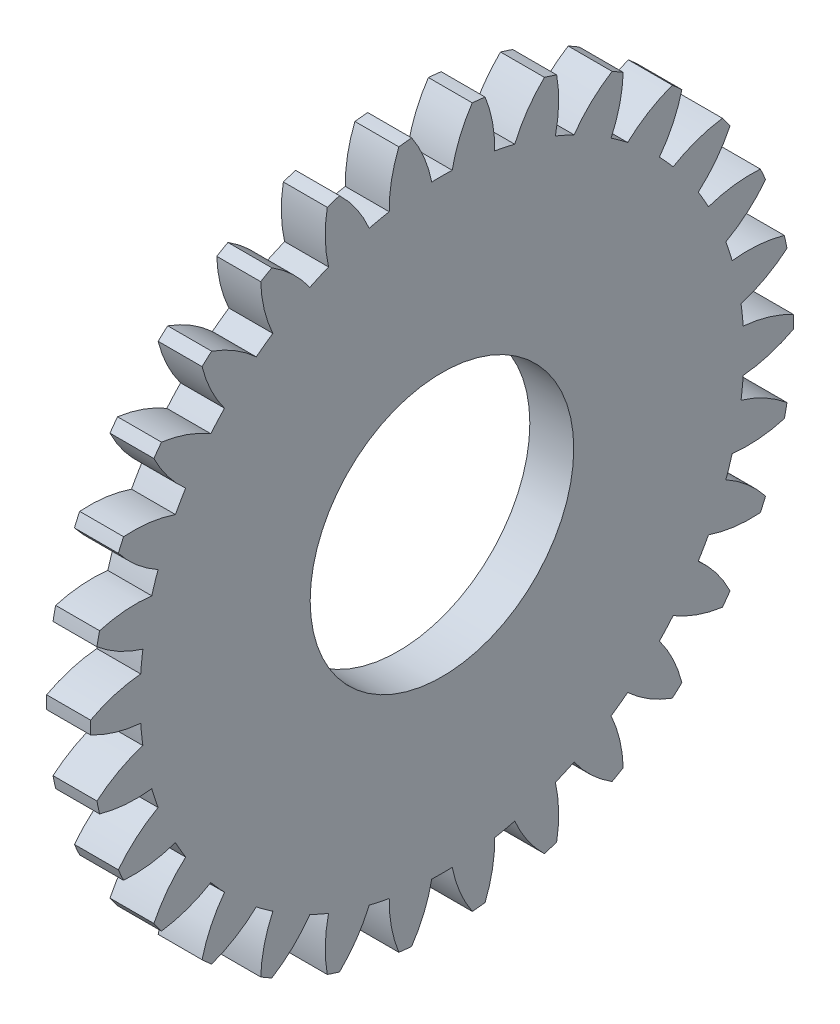
SolidWorks part; units mm, degrees
ref_plane "Plane1" through (0, 0, 0) normal (0, 0, 1) x (1, 0, 0)
ref_plane "Plane2" through (0, 0, 0) normal (0, 1, 0) x (1, 0, 0)
ref_plane "Plane3" through (0, 0, 0) normal (1, 0, 0) x (0, 0, -1)
other "Configuration Table"
sketch "HoldingSke" plane through (0, 0, 0) normal (0, 1, 0) x (1, 0, 0)
  line L0 (0, 0) -> (0.866, -0.5)
  line L1 (-15, 0) -> (100, 0) construction
  line L2 (0, 0) -> (-2.1039, 2.3779)
  line L3 (0, 0) -> (-11.863, 4.5341)
  line L4 (0, 0) -> (7.479, 4.318)
  line L5 (0, 0) -> (-46.8476, -17.4728)
  line L6 (0, 0) -> (-1.6579, -1.1186)
  line L7 (-2.1039, 2.3779) -> (8.6586, 51.2059)
  line L8 (-76.2, 54.61) -> (-73.9, 54.61)
  line L9 (-71.009, 38.7566) -> (-53.1078, 45.2721)
  line L10 (-76.2, 71.12) -> (104.1128, 71.12)
  line L11 (0, 0) -> (-2, 0)
  line L12 (-76.2, 101.6) -> (-76.162, 101.6)
  line L13 (24.9733, 27.94) -> (52.9518, 28.4284)
  line L14 (24.9733, 27.94) -> (24.9743, 27.94)
  line L15 (24.9733, 27.94) -> (100.4006, 29.5858)
  line L16 (-63.627, -1) -> (-12.827, -1)
  circle A0 centre (0, 0) radius 6
  circle A1 centre (0, 0) radius 13.749
  circle A2 centre (0, 0) radius 37.5
  circle A3 centre (0, 0) radius 6
  dimension "MHD" = 27.498
  dimension "Hub_dia" = 75
  dimension "Bore" = 12
  dimension "MBD" = 12
  dimension "Num_teeth" = 30
  dimension "Pitch" = 1
  dimension "Overall_len" = 50
  dimension "Show_teeth" = 30
  dimension "Thickness" = 2
  dimension "OAL" = 50.0001
  dimension "T_dim" = 2.3
  dimension "Ap" = 20
  dimension "H" = 19.05
  dimension "Pitch_radius" = 180.3128
  dimension "Width" = 2
  dimension "Backlash" = 0.038
  dimension "Addendum_fac" = 1
  dimension "Dedendum_fac" = 1.25
  dimension "Clearance_fac" = 0.25
  dimension "Dedendum_add" = 0.001
  dimension "Module" = 1
sketch "BasProSke" plane through (0, 0, 0) normal (0, 1, 0) x (1, 0, 0)
  line L0 (-10, 0) -> (60, 0) construction
  line L1 (0, 0) -> (0, 16)
  line L2 (0, 0) -> (2, 0)
  line L3 (2, 0) -> (2, 16)
  line L4 (2, 16) -> (0, 16)
  dimension "Thickness" = 2
  dimension "Diameter" = 32
revolve "Base-Revolve" add sketch "BasProSke" angle 360 about L0
sketch "TooCutSke" plane through (0, 0, 0) normal (1, 0, 0) x (0, 0, -1)
  line L1 (0, 0) -> (0, 107) construction
  line L2 (0, 0) -> (-0.8515, 14.9758) construction
  line L3 (0, 0) -> (-3.1323, 29.8014) construction
  line L4 (-0.8515, 14.9758) -> (-1.5661, 14.9007) construction
  arc A0 (0.4664, 13.7411) -> (-0.4664, 13.7411) centre (0, 0) ccw
  arc A1 (1.3975, 15.9644) -> (-1.3975, 15.9644) centre (0, 0) ccw
  circle A2 centre (0, 0) radius 15 construction
  circle A3 centre (0, 0) radius 14.0954 construction
  arc A4 (-0.4664, 13.7411) -> (-1.3975, 15.9644) centre (-6.3534, 12.5823) ccw
  arc A5 (1.3975, 15.9644) -> (0.4664, 13.7411) centre (6.3534, 12.5823) ccw
  dimension "Root_dia" = 27.498
  dimension "Overcut_dia" = 32.0508
  dimension "Pitch_dia" = 30
  dimension "Base_dia" = 28.1908
  dimension "Flank_rad" = 6
  dimension "Half_ang" = 6
  dimension "Half_CT" = 0.7185
extrude "ToothCut" cut sketch "TooCutSke" along normal through all
fillet "Breaks" [suppressed] radius 0.02
fillet "RootFillets" [suppressed] radius 0.251
pattern_circular "TeethCuts" count 30 over 360 about axis through (0, 0, 0) along (1, 0, 0) of "ToothCut", "RootFillets", "Breaks"
sketch "HubNeaOneSke" plane through (0, 0, 0) normal (-1, 0, 0) x (0, 0, 1)
  circle A0 centre (0, 0) radius 13.749
  dimension "Diameter" = 27.498
extrude "HubNearOne" [suppressed] add sketch "HubNeaOneSke" along normal blind 48.0001
sketch "HubNeaBotSke" plane through (0, 0, 0) normal (-1, 0, 0) x (0, 0, 1)
  circle A0 centre (0, 0) radius 13.749
  dimension "Diameter" = 27.498
extrude "HubNearBoth" [suppressed] add sketch "HubNeaBotSke" along normal blind 24
ref_plane "FarPln" through (2, 0, 0) normal (1, 0, 0) x (0, 0, -1)
sketch "HubFarSke" plane through (2, 0, 0) normal (1, 0, 0) x (0, 0, -1)
  circle A0 centre (0, 0) radius 13.749
  dimension "Diameter" = 27.498
extrude "HubFar" [suppressed] add sketch "HubFarSke" along normal blind 24
sketch "BorSke" plane through (0, 0, 0) normal (1, 0, 0) x (0, 0, -1)
  circle A0 centre (0, 0) radius 6
  dimension "Diameter" = 12
extrude "Bore" cut sketch "BorSke" along normal mid plane 100.0001
sketch "KeySke" plane through (0, 0, 0) normal (1, 0, 0) x (0, 0, -1)
  line L0 (-2.5, 0) -> (-2.5, 8.3)
  line L1 (-2.5, 8.3) -> (2.5, 8.3)
  line L2 (2.5, 8.3) -> (2.5, 0)
  line L3 (0, 0) -> (0, 34) construction
  line L4 (-2.5, 0) -> (2.5, 0)
  dimension "Offset" = 8.3
  dimension "Width" = 5
extrude "Keyway" [suppressed] cut sketch "KeySke" along normal mid plane 100.0001
pattern_circular "Keyway2" [suppressed] count 2 every 90 about axis through (-10, 0, 0) along (1, 0, 0)
equation "' \"Module@HoldingSke\" = 6.35"
equation "' \"Num_teeth@HoldingSke\" = 12"
equation "' \"Ap@HoldingSke\" =  20"
equation "' \"Ap@HoldingSke\" = 20"
equation "' \"Width@HoldingSke\" = 0.5 * 25.4"
equation "' \"Hub_dia@HoldingSke\"= 1 * 25.4"
equation "' \"Hub_dia@HoldingSke\" = 1 * 25.4"
equation "' \"Overall_len@HoldingSke\" = 1.0 * 25.4"
equation "' \"Bore@HoldingSke\" = 0.75 * 25.4"
equation "' \"T_dim@HoldingSke\" = 0.1 * 25.4"
equation "' \"Width@KeySke\" = 0.25 * 25.4"
equation "' \"Show_teeth@HoldingSke\" = 13"
equation "' \"Backlash@HoldingSke\" = 0.009 * 25.4"
equation "' \"Addendum_fac@HoldingSke\" = 1.0"
equation "' \"Dedendum_fac@HoldingSke\" = 1.25"
equation "' \"Dedendum_add@HoldingSke\" = 0.00005 * 25.4"
equation "' \"Clearance_fac@HoldingSke\" = 0.25"
equation "\"Pitch@HoldingSke\" = 1 / \"Module@HoldingSke\""
equation "\"Overcut_dia@TooCutSke\" = (\"Num_teeth@HoldingSke\" + 2 * \"Addendum_fac@HoldingSke\") / \"Pitch@HoldingSke\" + 0.002 * 25.4"
equation "\"Pitch_dia@TooCutSke\" = \"Num_teeth@HoldingSke\" / \"Pitch@HoldingSke\""
equation "\"Base_dia@TooCutSke\" = \"Num_teeth@HoldingSke\" / \"Pitch@HoldingSke\" * cos((\"Ap@HoldingSke\"  * 3.14159265 / 180))"
equation "\"Root_dia@TooCutSke\" = (\"Num_teeth@HoldingSke\" + 2) / \"Pitch@HoldingSke\" - 2 * (\"Addendum_fac@HoldingSke\" + \"Dedendum_fac@HoldingSke\") / \"Pitch@HoldingSke\" - \"Dedendum_add@HoldingSke\" * 2"
equation "\"Half_ang@TooCutSke\" = 180 / \"Num_teeth@HoldingSke\""
equation "\"Half_CT@TooCutSke\" = \"Num_teeth@HoldingSke\" / \"Pitch@HoldingSke\" * sin((3.14159265 / 2 / \"Num_teeth@HoldingSke\")) / 2 - 7 * \"Backlash@HoldingSke\" / 4"
equation "\"Flank_rad@TooCutSke\" = \"Num_teeth@HoldingSke\" / \"Pitch@HoldingSke\" / 5"
equation "\"Radius@RootFillets\" = \"Clearance_fac@HoldingSke\" / \"Pitch@HoldingSke\" + \"Dedendum_add@HoldingSke\""
equation "\"Break_rad@Breaks\" = 0.02 / \"Pitch@HoldingSke\""
equation "\"Thickness@HoldingSke\" = \"Width@HoldingSke\""
equation "\"OAL@HoldingSke\" = \"Thickness@HoldingSke\""
equation "\"MHD@HoldingSke\" = (\"Num_teeth@HoldingSke\" + 2) / \"Pitch@HoldingSke\" - 2 * (\"Addendum_fac@HoldingSke\" + \"Dedendum_fac@HoldingSke\")  / \"Pitch@HoldingSke\" - \"Dedendum_add@HoldingSke\" * 2"
equation "\"MBD@HoldingSke\" = (\"Num_teeth@HoldingSke\" + 2) / \"Pitch@HoldingSke\" - 2 * (\"Addendum_fac@HoldingSke\" + \"Dedendum_fac@HoldingSke\")  / \"Pitch@HoldingSke\" - \"Dedendum_add@HoldingSke\" * 2 - 0.002 * 25.4"
equation "\"MHD@HoldingSke\" = ((sgn( \"MHD@HoldingSke\" - \"Hub_dia@HoldingSke\" )-1)*( \"MHD@HoldingSke\" - \"Hub_dia@HoldingSke\" ))/-2+ \"Hub_dia@HoldingSke\""
equation "\"MBD@HoldingSke\" = ((sgn( \"MBD@HoldingSke\" - \"Bore@HoldingSke\" )-1)*( \"MBD@HoldingSke\" - \"Bore@HoldingSke\" ))/-2+ \"Bore@HoldingSke\""
equation "\"OAL@HoldingSke\" = ((sgn( \"OAL@HoldingSke\" - \"Overall_len@HoldingSke\" )+1)*( \"OAL@HoldingSke\" - \"Overall_len@HoldingSke\" ))/2 + \"Overall_len@HoldingSke\" + 0.000002 * 25.4"
equation "\"Num_teeth@TeethCuts\" = int( \"Show_teeth@HoldingSke\" ) + 1"
equation "\"Num_teeth@TeethCuts\" = ((sgn( \"Num_teeth@TeethCuts\" - \"Num_teeth@HoldingSke\" )-1)*( \"Num_teeth@TeethCuts\" - \"Num_teeth@HoldingSke\" ))/-2+ \"Num_teeth@HoldingSke\""
equation "\"Num_teeth@TeethCuts\" = ((sgn( \"Num_teeth@TeethCuts\" - 2.0)+1)*( \"Num_teeth@TeethCuts\" - 2.0))/2 +2.0"
equation "\"Angle@TeethCuts\" = 360.0 / \"Num_teeth@HoldingSke\""
equation "\"Diameter@BasProSke\" = (\"Num_teeth@HoldingSke\" + 2 * \"Addendum_fac@HoldingSke\") / \"Pitch@HoldingSke\""
equation "\"Thickness@BasProSke\"  = \"Thickness@HoldingSke\""
equation "' \"Fillet_rad@BasProSke\" =  \"Thickness@HoldingSke\" * 0.05"
equation "' \"Fillet_rad@BasProSke\" = \"Thickness@HoldingSke\" * 0.05"
equation "\"MHD@HoldingSke\" = ((sgn( \"MHD@HoldingSke\" - \"Root_dia@TooCutSke\" )-1)*( \"MHD@HoldingSke\" - \"Root_dia@TooCutSke\" ))/-2+ \"Root_dia@TooCutSke\""
equation "\"Diameter@HubNeaOneSke\" = \"MHD@HoldingSke\""
equation "\"Length@HubNearOne\" = \"OAL@HoldingSke\" - \"Thickness@BasProSke\""
equation "\"Diameter@HubNeaBotSke\" = \"MHD@HoldingSke\""
equation "\"Length@HubNearBoth\" = ( \"OAL@HoldingSke\" - \"Thickness@BasProSke\" ) / 2.0"
equation "\"Thickness@FarPln\" = \"Thickness@BasProSke\""
equation "\"Diameter@HubFarSke\" = \"MHD@HoldingSke\""
equation "\"Length@HubFar\" = ( \"OAL@HoldingSke\" - \"Thickness@BasProSke\" ) / 2.0"
equation "\"Diameter@BorSke\" = \"MBD@HoldingSke\""
equation "\"D1@Bore\" = \"OAL@HoldingSke\" * 2.0"
equation "\"D1@Keyway\" = \"OAL@HoldingSke\" * 2.0"
equation "\"Offset@KeySke\" = \"T_dim@HoldingSke\" + \"MBD@HoldingSke\" / 2.0"
